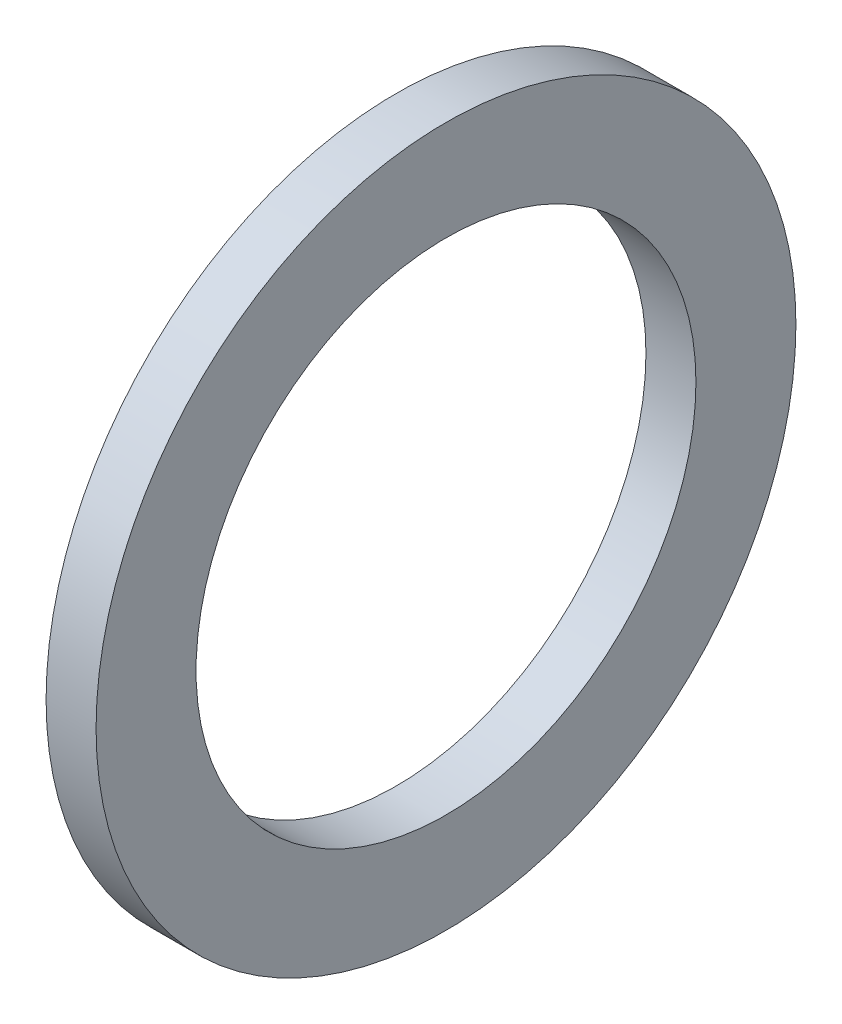
SolidWorks part; units mm, degrees
ref_plane "前视基准面" through (0, 0, 0) normal (0, 0, 1) x (1, 0, 0)
ref_plane "上视基准面" through (0, 0, 0) normal (0, 1, 0) x (1, 0, 0)
ref_plane "右视基准面" through (0, 0, 0) normal (1, 0, 0) x (0, 0, -1)
sketch "草图1" plane through (0, 0, 0) normal (1, 0, 0) x (0, 0, -1)
  circle A0 centre (0, 0) radius 2.5
  circle A1 centre (0, 0) radius 3.5
  dimension "D1" = 5
  dimension "D2" = 7
extrude "凸台-拉伸1" add sketch "草图1" along normal blind 0.5
